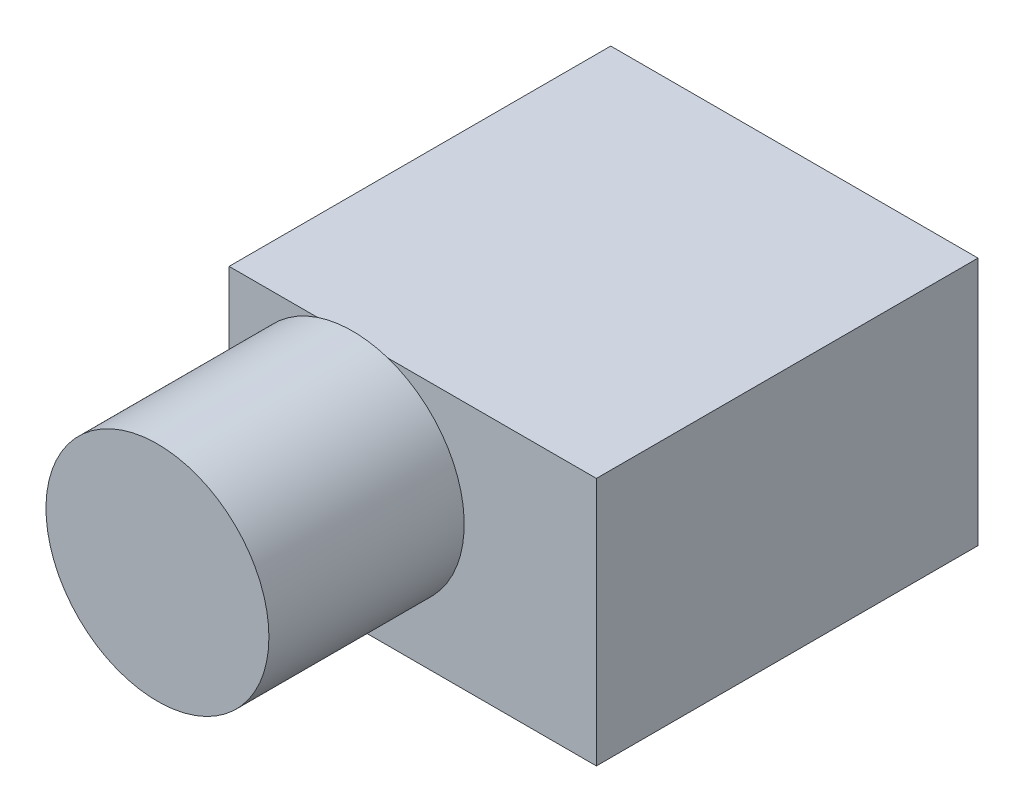
SolidWorks part; units mm, degrees
ref_plane "Front Plane" through (0, 0, 0) normal (0, 0, 1) x (1, 0, 0)
ref_plane "Top Plane" through (0, 0, 0) normal (0, 1, 0) x (1, 0, 0)
ref_plane "Right Plane" through (0, 0, 0) normal (1, 0, 0) x (0, 0, -1)
sketch "Sketch1" plane through (0, 0, 0) normal (0, 1, 0) x (1, 0, 0)
  line L1 (-10.25, -10.65) -> (10.25, -10.65)
  line L2 (-10.25, -10.65) -> (-10.25, 10.65)
  line L3 (-10.25, 10.65) -> (10.25, 10.65)
  line L4 (10.25, -10.65) -> (10.25, 10.65)
  line L5 (-10.25, -10.65) -> (10.25, 10.65) construction
  line L6 (-10.25, 10.65) -> (10.25, -10.65) construction
  point P0 (0, 0)
  dimension "D1" = 21.3
  dimension "D2" = 20.5
extrude "Boss-Extrude1" add sketch "Sketch1" along normal blind 13.9
sketch "Sketch2" plane through (0, 0, 10.65) normal (0, 0, 1) x (1, 0, 0)
  circle A0 centre (-3.3498, 7.9962) radius 6.222
extrude "Boss-Extrude2" add sketch "Sketch2" along normal blind 10.9
